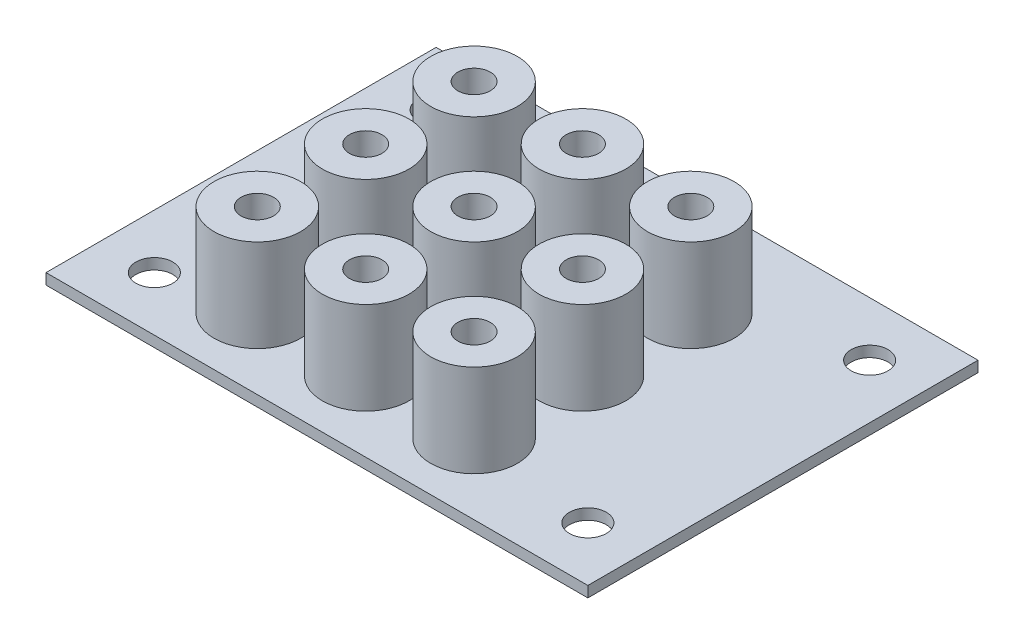
SolidWorks part; units mm, degrees
ref_plane "Front Plane" through (0, 0, 0) normal (0, 0, 1) x (1, 0, 0)
ref_plane "Top Plane" through (0, 0, 0) normal (0, 1, 0) x (1, 0, 0)
ref_plane "Right Plane" through (0, 0, 0) normal (1, 0, 0) x (0, 0, -1)
sketch "Sketch1" plane through (0, 0, 0) normal (0, 1, 0) x (1, 0, 0)
  line L0 (45, 31) -> (5, 31) construction
  line L1 (0, 0) -> (50, 0)
  line L2 (0, 0) -> (0, 36)
  line L3 (0, 36) -> (50, 36)
  line L4 (50, 0) -> (50, 36)
  line L6 (45, 31) -> (45, 5) construction
  circle A19 centre (13, 6.5) radius 1.25
  circle A28 centre (5, 5) radius 1.7
  circle A29 centre (5, 31) radius 1.7
  circle A30 centre (45, 31) radius 1.7
  circle A31 centre (45, 5) radius 1.7
  circle A32 centre (23, 6.5) radius 1.25
  circle A33 centre (33, 6.5) radius 1.25
  circle A34 centre (23, 16.5) radius 1.25
  circle A35 centre (33, 16.5) radius 1.25
  circle A36 centre (23, 26.5) radius 1.25
  circle A37 centre (33, 26.5) radius 1.25
  circle A38 centre (13, 16.5) radius 1.25
  circle A39 centre (13, 26.5) radius 1.25
  point P7 (45, 18)
  point P9 (25, 31)
  point P10 (25, 36)
  point P20 (50, 18)
  dimension "D5" = 40
  dimension "D6" = 26
  dimension "D3" = 2.5
  dimension "D8" = 3.4
  dimension "D1" = 50
  dimension "D2" = 36
  dimension "D4" = 8
  dimension "D7" = 1.5
  dimension "D9" = 3
extrude "Boss-Extrude1" add sketch "Sketch1" along normal blind 1
sketch "Sketch2" plane through (0, 1, 0) normal (0, 1, 0) x (1, 0, 0)
  circle A0 centre (13, 26.5) radius 1.5
  circle A1 centre (13, 26.5) radius 1.25 construction
  circle A2 centre (13, 26.5) radius 4
  circle A3 centre (23, 26.5) radius 4
  circle A4 centre (23, 26.5) radius 1.5
  circle A5 centre (33, 26.5) radius 4
  circle A6 centre (33, 26.5) radius 1.5
  circle A7 centre (23, 16.5) radius 4
  circle A8 centre (23, 16.5) radius 1.5
  circle A9 centre (33, 16.5) radius 4
  circle A10 centre (33, 16.5) radius 1.5
  circle A11 centre (23, 6.5) radius 4
  circle A12 centre (23, 6.5) radius 1.5
  circle A13 centre (33, 6.5) radius 4
  circle A14 centre (33, 6.5) radius 1.5
  circle A15 centre (13, 16.5) radius 4
  circle A16 centre (13, 16.5) radius 1.5
  circle A17 centre (13, 6.5) radius 4
  circle A18 centre (13, 6.5) radius 1.5
  dimension "D1" = 3
  dimension "D2" = 8
extrude "Boss-Extrude2" add sketch "Sketch2" along normal blind 8.525
equation "\"o\"= 10mm"
equation "\"P\"= 10"
